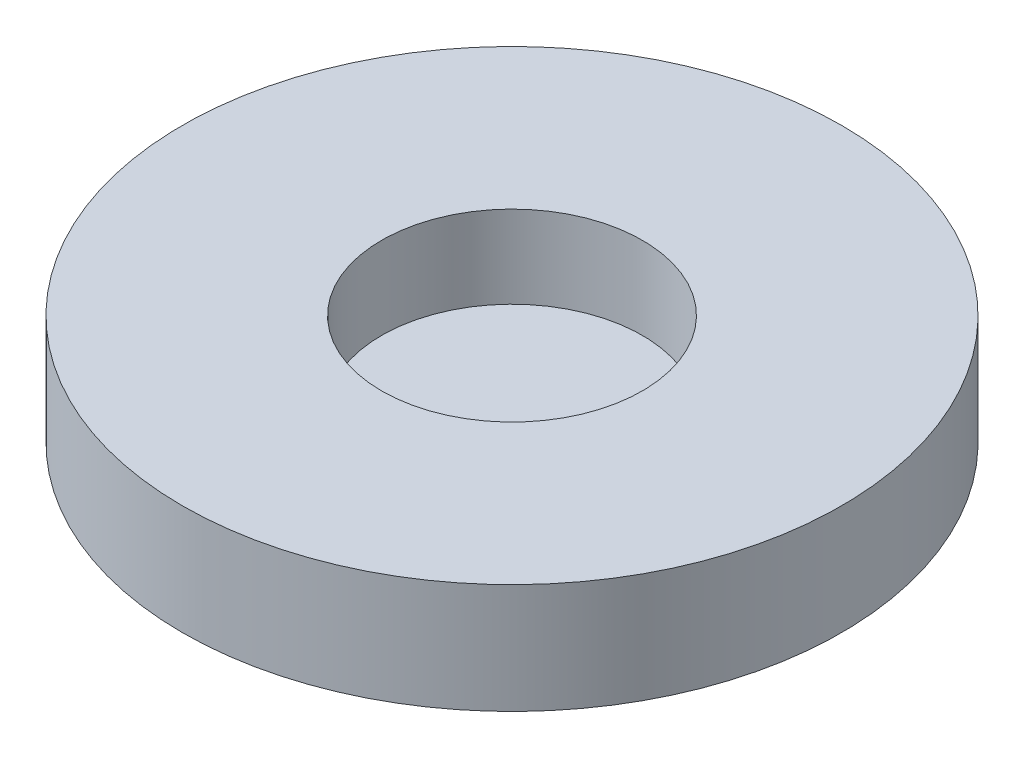
SolidWorks part; units mm, degrees
ref_plane "Front Plane" through (0, 0, 0) normal (0, 0, 1) x (1, 0, 0)
ref_plane "Top Plane" through (0, 0, 0) normal (0, 1, 0) x (1, 0, 0)
ref_plane "Right Plane" through (0, 0, 0) normal (1, 0, 0) x (0, 0, -1)
sketch "Sketch1" plane through (0, 0, 0) normal (0, 1, 0) x (1, 0, 0)
  circle A0 centre (0, 0) radius 38.1
  dimension "D1" = 76.2
extrude "Boss-Extrude1" add sketch "Sketch1" along normal blind 12.7
sketch "Sketch2" plane through (0, 12.7, 0) normal (0, 1, 0) x (1, 0, 0)
  circle A0 centre (0, 0) radius 15.0813
  dimension "D1" = 30.1625
extrude "Cut-Extrude1" cut sketch "Sketch2" against normal blind 9.525
